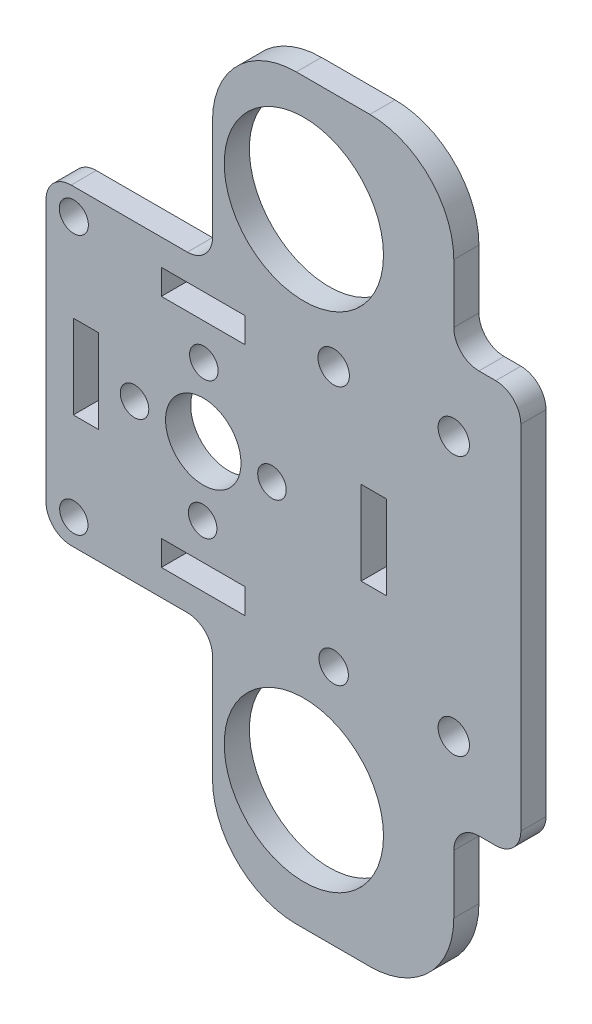
SolidWorks part; units mm, degrees
ref_plane "Front Plane" through (0, 0, 0) normal (0, 0, 1) x (1, 0, 0)
ref_plane "Top Plane" through (0, 0, 0) normal (0, 1, 0) x (1, 0, 0)
ref_plane "Right Plane" through (0, 0, 0) normal (1, 0, 0) x (0, 0, -1)
sketch "Sketch1" plane through (0, 0, 0) normal (0, 0, 1) x (1, 0, 0)
  line L0 (147.062, -92.9701) -> (147.062, -71.8565)
  line L1 (147.062, -92.9701) -> (127.2038, -92.9701)
  line L2 (127.2038, -92.9701) -> (127.2038, -111.5917)
  line L4 (147.062, -151.8871) -> (147.062, -155.8871)
  line L5 (145.9607, -111.5917) -> (157.9607, -111.5917) construction
  line L6 (157.9607, -111.5917) -> (157.9607, -81.5917) construction
  line L7 (157.9607, -111.5917) -> (157.9607, -141.5917) construction
  line L8 (147.062, -71.8565) -> (147.062, -67.8565)
  line L9 (127.2038, -111.5917) -> (127.2038, -130.2155)
  line L10 (127.2038, -130.2155) -> (147.062, -130.2155)
  line L11 (147.062, -130.2155) -> (147.062, -151.8871)
  line L13 (147.062, -67.8565) -> (175.8433, -67.8565)
  line L14 (147.062, -155.8871) -> (175.8433, -155.8871)
  line L15 (175.8433, -67.8565) -> (175.8433, -87.8565)
  line L16 (175.8433, -155.8871) -> (175.8433, -135.8871)
  line L17 (175.8433, -87.8565) -> (183.8433, -87.8565)
  line L18 (175.8433, -135.8871) -> (183.8433, -135.8871)
  line L19 (183.8433, -87.8565) -> (183.8433, -135.8871)
  line L20 (145.9607, -111.5917) -> (131.9607, -111.5917) construction
  line L21 (145.9607, -111.5917) -> (145.9607, -97.5917) construction
  line L22 (145.9607, -111.5917) -> (145.9607, -125.5917) construction
  line L23 (157.9607, -111.5917) -> (166.2936, -111.5917) construction
  line L24 (130.4607, -106.5917) -> (133.4607, -106.5917)
  line L25 (130.4607, -106.5917) -> (130.4607, -116.5917)
  line L26 (130.4607, -116.5917) -> (133.4607, -116.5917)
  line L27 (133.4607, -106.5917) -> (133.4607, -116.5917)
  line L28 (130.4607, -106.5917) -> (133.4607, -116.5917) construction
  line L29 (130.4607, -116.5917) -> (133.4607, -106.5917) construction
  line L30 (140.9607, -99.0917) -> (150.9607, -99.0917)
  line L31 (140.9607, -99.0917) -> (140.9607, -96.0917)
  line L32 (140.9607, -96.0917) -> (150.9607, -96.0917)
  line L33 (150.9607, -99.0917) -> (150.9607, -96.0917)
  line L34 (140.9607, -99.0917) -> (150.9607, -96.0917) construction
  line L35 (140.9607, -96.0917) -> (150.9607, -99.0917) construction
  line L36 (140.9607, -127.0917) -> (150.9607, -127.0917)
  line L37 (140.9607, -127.0917) -> (140.9607, -124.0917)
  line L38 (140.9607, -124.0917) -> (150.9607, -124.0917)
  line L39 (150.9607, -127.0917) -> (150.9607, -124.0917)
  line L40 (140.9607, -127.0917) -> (150.9607, -124.0917) construction
  line L41 (140.9607, -124.0917) -> (150.9607, -127.0917) construction
  line L43 (164.7936, -106.5917) -> (167.7936, -106.5917)
  line L44 (164.7936, -106.5917) -> (164.7936, -116.5917)
  line L45 (164.7936, -116.5917) -> (167.7936, -116.5917)
  line L46 (167.7936, -106.5917) -> (167.7936, -116.5917)
  line L47 (164.7936, -106.5917) -> (167.7936, -116.5917) construction
  line L48 (164.7936, -116.5917) -> (167.7936, -106.5917) construction
  circle A0 centre (130.52, -96.082) radius 1.7379
  circle A2 centre (161.52, -96.082) radius 1.8732
  circle A3 centre (130.52, -127.1142) radius 1.6901
  circle A4 centre (161.52, -127.082) radius 1.7542
  circle A5 centre (154.1576, -111.6623) radius 1.7
  circle A6 centre (145.8901, -119.7886) radius 1.7
  circle A7 centre (137.7638, -111.5212) radius 1.7
  circle A8 centre (146.0313, -103.3948) radius 1.7
  circle A10 centre (145.9607, -111.5917) radius 4.5
  circle A12 centre (175.8433, -96.1142) radius 1.87
  circle A15 centre (157.9607, -81.5917) radius 9.5
  circle A16 centre (157.9607, -141.5917) radius 9.5
  circle A17 centre (175.8433, -127.1142) radius 1.87
  point P44 (145.9607, -111.5917)
  point P47 (106.5258, -71.8662)
  dimension "D1" = 4
  dimension "D4" = 12
  dimension "D5" = 4
  dimension "D10" = 4
  dimension "D2" = 30
  dimension "D3" = 30
  dimension "D6" = 20
  dimension "D7" = 20
  dimension "D8" = 8
  dimension "D9" = 8
  dimension "D11" = 14
  dimension "D12" = 14
  dimension "D13" = 14
  dimension "D14" = 3
  dimension "D15" = 3
  dimension "D16" = 3
  dimension "D17" = 10
  dimension "D18" = 10
  dimension "D19" = 10
  dimension "D20" = 3
  dimension "D21" = 10
extrude "Boss-Extrude1" add sketch "Sketch1" along normal blind 3
fillet "Fillet1" radius 3 8 edges at (175.8433, -135.8871, 1.5) (183.8433, -135.8871, 1.5) (183.8433, -87.8565, 1.5) (175.8433, -87.8565, 1.5) (127.2038, -92.9701, 1.5) (127.2038, -130.2155, 1.5) (147.062, -130.2155, 1.5) (147.062, -92.9701, 1.5)
fillet "Fillet2" radius 10 4 edges at (147.062, -67.8565, 1.5) (147.062, -155.8871, 1.5) (175.8433, -155.8871, 1.5) (175.8433, -67.8565, 1.5)
